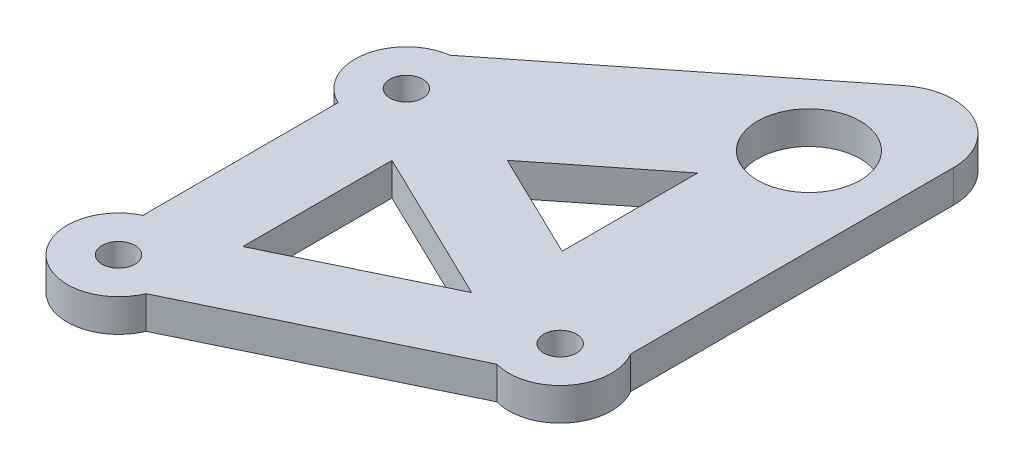
SolidWorks part; units mm, degrees
ref_plane "Front Plane" through (0, 0, 0) normal (0, 0, 1) x (1, 0, 0)
ref_plane "Top Plane" through (0, 0, 0) normal (0, 1, 0) x (1, 0, 0)
ref_plane "Right Plane" through (0, 0, 0) normal (1, 0, 0) x (0, 0, -1)
sketch "Sketch1" plane through (0, 0, 0) normal (0, 1, 0) x (1, 0, 0)
  line L0 (-14.5, 14.02) -> (-14.5, -14.02) construction
  line L5 (-9.1487, 7.2677) -> (5.8843, 0)
  line L7 (-14.5, -14.02) -> (14.5, 0) construction
  line L8 (14.5, 0) -> (-14.5, 14.02) construction
  line L9 (-16.6487, -9.5052) -> (-16.6487, 9.5052)
  line L11 (-9.1487, -7.2677) -> (-9.1487, 7.2677)
  line L12 (-3.5432, 12.8882) -> (6.8076, 7.8841)
  line L13 (14.5, 0) -> (-14.5, 0) construction
  line L14 (13.1547, -4.8156) -> (-9.8903, -15.9567)
  line L15 (-9.1487, -7.2677) -> (5.8843, 0)
  line L16 (-1.6322, 3.6338) -> (-5.1537, 0) construction
  line L17 (-5.1537, 0) -> (-1.6322, -3.6338) construction
  line L18 (-15.1859, 18.9727) -> (9.4885, 38.5275)
  line L19 (-3.5432, 12.8882) -> (6.8076, 21.0914)
  line L20 (18.8076, 2.5386) -> (18.8076, 34.0222)
  line L21 (6.8076, 7.8841) -> (6.8076, 21.0914)
  line L22 (-1.6322, 3.6338) -> (17.4194, 43.0416) construction
  line L23 (-2.8487, 28.7501) -> (6.8076, 21.0914) construction
  line L24 (18.8076, 18.2804) -> (6.8076, 21.0914) construction
  line L25 (15.5611, 39.1977) -> (10.3381, 28.394) construction
  arc A0 (-16.6487, -9.5052) -> (-9.8903, -15.9567) centre (-14.5, -14.02) ccw
  arc A3 (-15.1859, 18.9727) -> (-16.6487, 9.5052) centre (-14.5, 14.02) ccw
  arc A4 (13.1547, -4.8156) -> (18.8076, 2.5386) centre (14.5, 0) ccw
  arc A5 (9.4885, 38.5275) -> (18.8076, 34.0222) centre (13.059, 34.0222) cw
  point P0 (0, 0)
  point P8 (-14.5, 0)
  point P14 (1.6322, 10.3862)
  point P16 (0, 0)
  point P32 (0, 0)
  point P33 (0, 0)
  point P34 (0, 0)
  dimension "D1" = 10
  dimension "D10" = 5.7486
  dimension "D11" = 5
  dimension "D12" = 5
  dimension "D2" = 28.04
  dimension "D3" = 29
  dimension "D4" = 7.5
  dimension "D5" = 7.5
  dimension "D6" = 3.75
  dimension "D7" = 7.5
  dimension "D8" = 12
  dimension "D9" = 12
  dimension "D13" = 12
extrude "Boss-Extrude1" add sketch "Sketch1" along normal blind 3.18
hole_wizard "Ø3.2 (3.2) Diameter Hole1" positions "Sketch7" profile "Sketch8" hole size "Ø3.2" standard "ANSI Metric" end condition up to next
sketch "Sketch7" plane through (0, 3.18, 0) normal (0, -1, 0) x (-1, 0, 0)
  point P0 (-14.5, 0)
  point P3 (14.5, -14.02)
  point P6 (14.5, 14.02)
sketch "Sketch8" plane through (14.5, 3.18, 0) normal (1, 0, 0) x (0, 0, 1)
  line L0 (0, 0) -> (0, 3.18)
  line L1 (0, 3.18) -> (1.6, 3.18)
  line L2 (1.6, 3.18) -> (1.6, 0)
  line L5 (1.6, 0) -> (0, 0)
  line L11 (0, -6.35) -> (0, 107.95) construction
  dimension "Thru Hole Dia." = 3.2
  dimension "Thru Hole Depth" = 3.18
hole_wizard "Ø10.0 (10) Diameter Hole1" positions "Sketch15" profile "Sketch14" hole size "Ø10.0" standard "ANSI Metric" end condition up to next
sketch "Sketch15" plane through (0, 0, 0) normal (0, -1, 0) x (-1, 0, 0)
  point P0 (-10.3381, 28.394)
sketch "Sketch14" plane through (10.3381, 0, -28.394) normal (1, 0, 0) x (0, 0, -1)
  line L0 (0, 0) -> (0, 3.18)
  line L1 (0, 3.18) -> (5, 3.18)
  line L2 (5, 3.18) -> (5, 0)
  line L5 (5, 0) -> (0, 0)
  line L11 (0, -6.35) -> (0, 107.95) construction
  dimension "Thru Hole Dia." = 10
  dimension "Thru Hole Depth" = 3.18
